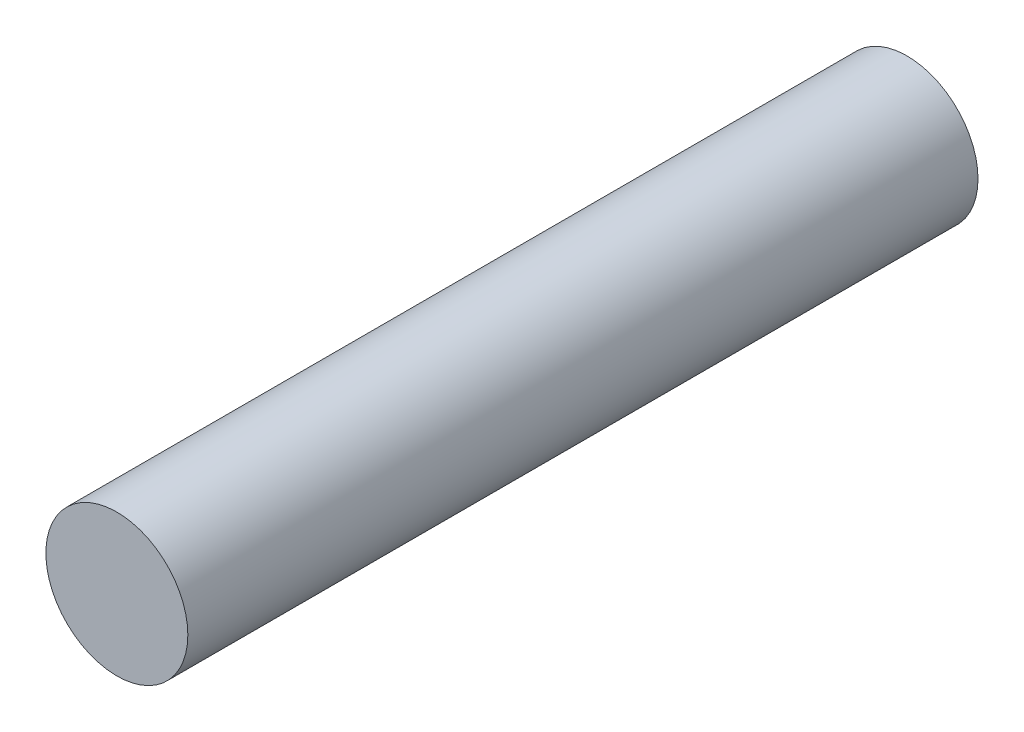
SolidWorks part; units mm, degrees
material "6061-T6 (SS)"
ref_plane "Front Plane" through (0, 0, 0) normal (0, 0, 1) x (1, 0, 0)
ref_plane "Top Plane" through (0, 0, 0) normal (0, 1, 0) x (1, 0, 0)
ref_plane "Right Plane" through (0, 0, 0) normal (1, 0, 0) x (0, 0, -1)
sketch "Sketch1" plane through (0, 0, 0) normal (0, 0, 1) x (1, 0, 0)
  circle A0 centre (0, 0) radius 18.2563
  dimension "D1" = 36.5125
extrude "Boss-Extrude1" add sketch "Sketch1" along normal mid plane 203.2
chamfer "Chamfer1" [suppressed] distance 25.4 distance2 3.9688
chamfer "Chamfer2" [suppressed] distance 3.9688 distance2 25.4
